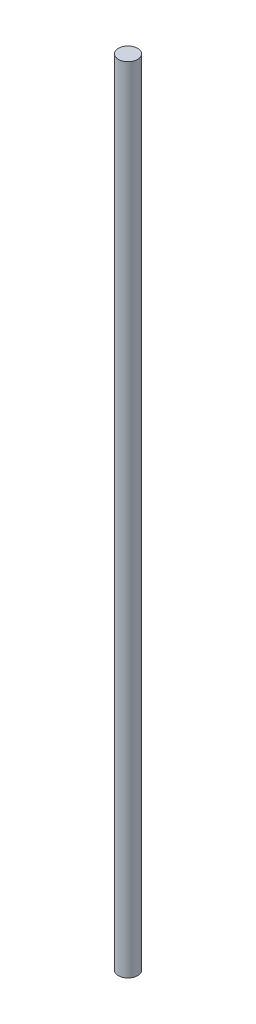
SolidWorks part; units mm, degrees
ref_plane "前视基准面" through (0, 0, 0) normal (0, 0, 1) x (1, 0, 0)
ref_plane "上视基准面" through (0, 0, 0) normal (0, 1, 0) x (1, 0, 0)
ref_plane "右视基准面" through (0, 0, 0) normal (1, 0, 0) x (0, 0, -1)
ref_plane "基准面4" through (0, 0, 0) normal (0, 0, -1) x (-1, 0, 0)
sketch "草图1" plane through (0, 0, 0) normal (0, 0, -1) x (-1, 0, 0)
  line L0 (-104, -330) -> (-100, -330)
  line L1 (-100, -330) -> (-100, 0)
  line L2 (-100, 0) -> (-104, 0)
  line L3 (-104, 0) -> (-104, -330)
  line L4 (-100, -330) -> (-100, 0) construction
revolve "旋转1" add sketch "草图1" angle 360 about L4
